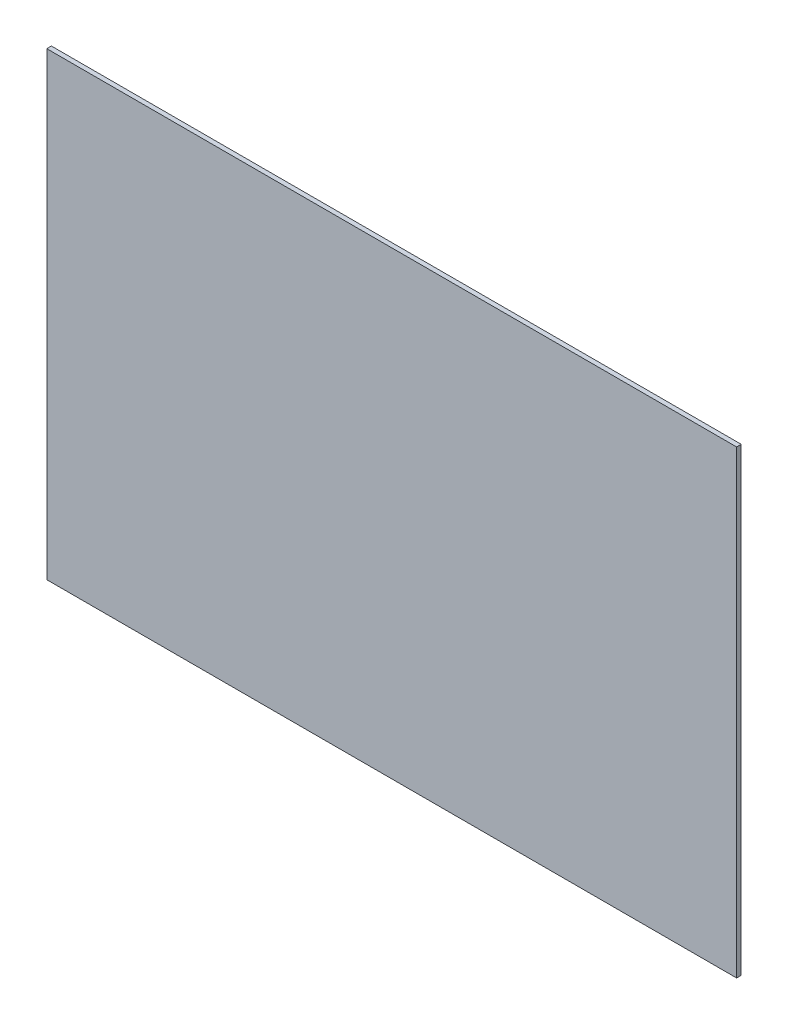
SolidWorks part; units mm, degrees
ref_plane "Front Plane" through (0, 0, 0) normal (0, 0, 1) x (1, 0, 0)
ref_plane "Top Plane" through (0, 0, 0) normal (0, 1, 0) x (1, 0, 0)
ref_plane "Right Plane" through (0, 0, 0) normal (1, 0, 0) x (0, 0, -1)
sketch "Sketch1" plane through (0, 0, 0) normal (0, 0, 1) x (1, 0, 0)
  line L1 (-750, -500) -> (750, -500)
  line L2 (-750, -500) -> (-750, 500)
  line L3 (-750, 500) -> (750, 500)
  line L4 (750, -500) -> (750, 500)
  line L5 (-750, -500) -> (750, 500) construction
  line L6 (-750, 500) -> (750, -500) construction
  point P0 (0, 0)
  dimension "D1" = 1000
  dimension "D2" = 1500
extrude "Boss-Extrude1" add sketch "Sketch1" along normal blind 10
